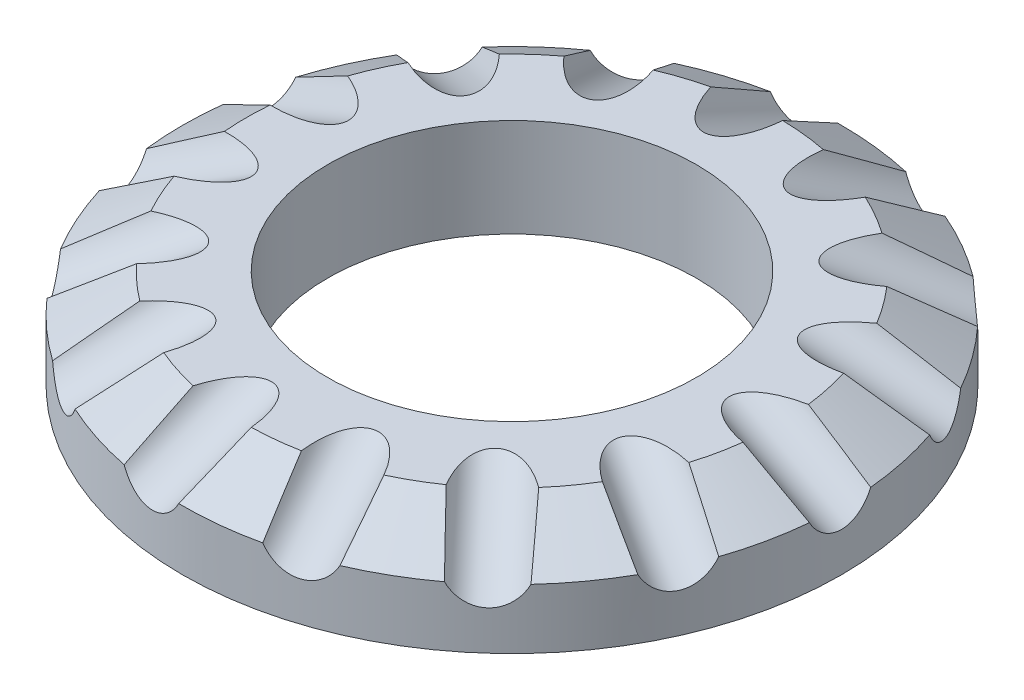
SolidWorks part; units mm, degrees
ref_plane "Ebene vorne" through (0, 0, 0) normal (0, 0, 1) x (1, 0, 0)
ref_plane "Ebene oben" through (0, 0, 0) normal (0, 1, 0) x (1, 0, 0)
ref_plane "Ebene rechts" through (0, 0, 0) normal (1, 0, 0) x (0, 0, -1)
sketch "Skizze1" plane through (0, 0, 0) normal (0, 0, 1) x (1, 0, 0)
  line L0 (16.1448, 0) -> (16.1448, 8.6081)
  line L1 (16.1448, 8.6081) -> (23.2614, 8.6081)
  line L2 (23.2614, 8.6081) -> (28.845, 5.2346)
  line L3 (28.845, 5.2346) -> (28.845, 0)
  line L4 (28.845, 0) -> (16.1448, 0)
  line L5 (0, 0) -> (0, 20.9386) construction
revolve "Rotation1" add sketch "Skizze1" angle 360 about L5
sketch "Skizze2" plane through (0, 0, 0) normal (0, 0, 1) x (1, 0, 0)
  line L0 (14.2629, 14.6362) -> (33.803, 4.3561) construction
  line L1 (18.434, 12.4418) -> (35.219, 3.6111)
  line L2 (18.434, 12.4418) -> (16.9826, 9.6831)
  line L3 (35.219, 3.6111) -> (33.7676, 0.8524)
  line L4 (16.9826, 9.6831) -> (33.7676, 0.8524)
revolve "Schnitt-Rotation1" cut sketch "Skizze2" angle 360 about L0
pattern_circular "Kreismuster1" count 15 over 360 about axis through (0, 0, 0) along (0, -1, 0) of "Schnitt-Rotation1"
